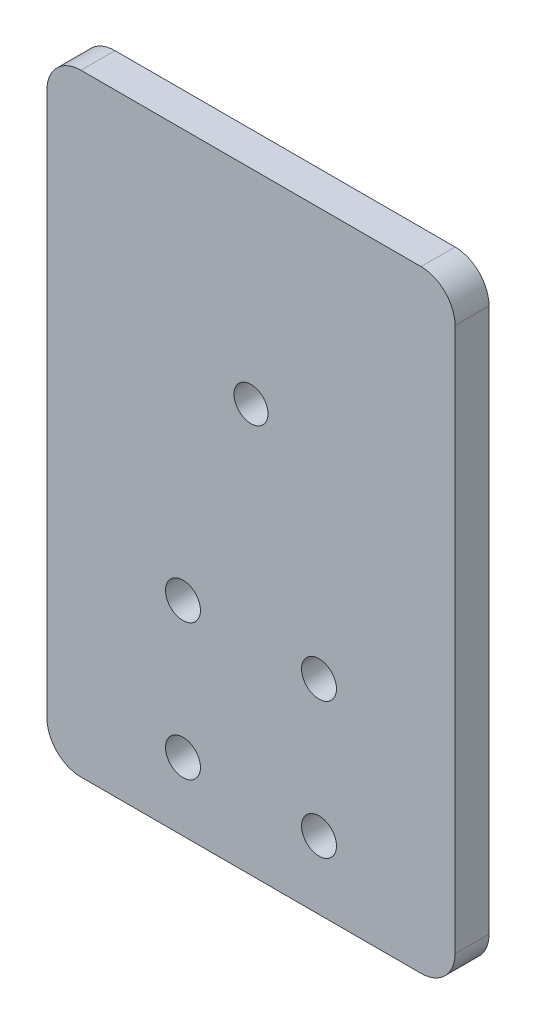
SolidWorks part; units mm, degrees
ref_plane "Front Plane" through (0, 0, 0) normal (0, 0, 1) x (1, 0, 0)
ref_plane "Top Plane" through (0, 0, 0) normal (0, 1, 0) x (1, 0, 0)
ref_plane "Right Plane" through (0, 0, 0) normal (1, 0, 0) x (0, 0, -1)
sketch "Sketch1" plane through (0, 0, 0) normal (0, 0, 1) x (1, 0, 0)
  line L0 (25.4, 12.7) -> (50.8, 12.7) construction
  line L1 (0, 0) -> (76.2, 0)
  line L2 (0, 0) -> (0, 114.3)
  line L3 (0, 114.3) -> (76.2, 114.3)
  line L4 (76.2, 0) -> (76.2, 114.3)
  line L5 (25.4, 12.7) -> (25.4, 38.1) construction
  circle A0 centre (25.4, 12.7) radius 3.2639
  circle A1 centre (50.8, 12.7) radius 3.2639
  circle A2 centre (25.4, 38.1) radius 3.2639
  circle A3 centre (50.8, 38.1) radius 3.2639
  circle A4 centre (38.1, 76.2) radius 3.175
  dimension "D3" = 6.5278
  dimension "D10" = 6.35
  dimension "D1" = 114.3
  dimension "D2" = 76.2
  dimension "D4" = 12.7
  dimension "D5" = 25.4
  dimension "D6" = 90
  dimension "D7" = 25.4
  dimension "D8" = 12.7
  dimension "D9" = 25.4
  dimension "D11" = 38.1
  dimension "D12" = 38.1
extrude "Extrude1" add sketch "Sketch1" along normal blind 6.35
fillet "Fillet1" radius 6.35 4 edges at (76.2, 0, 3.175) (0, 0, 3.175) (0, 114.3, 3.175) (76.2, 114.3, 3.175)
